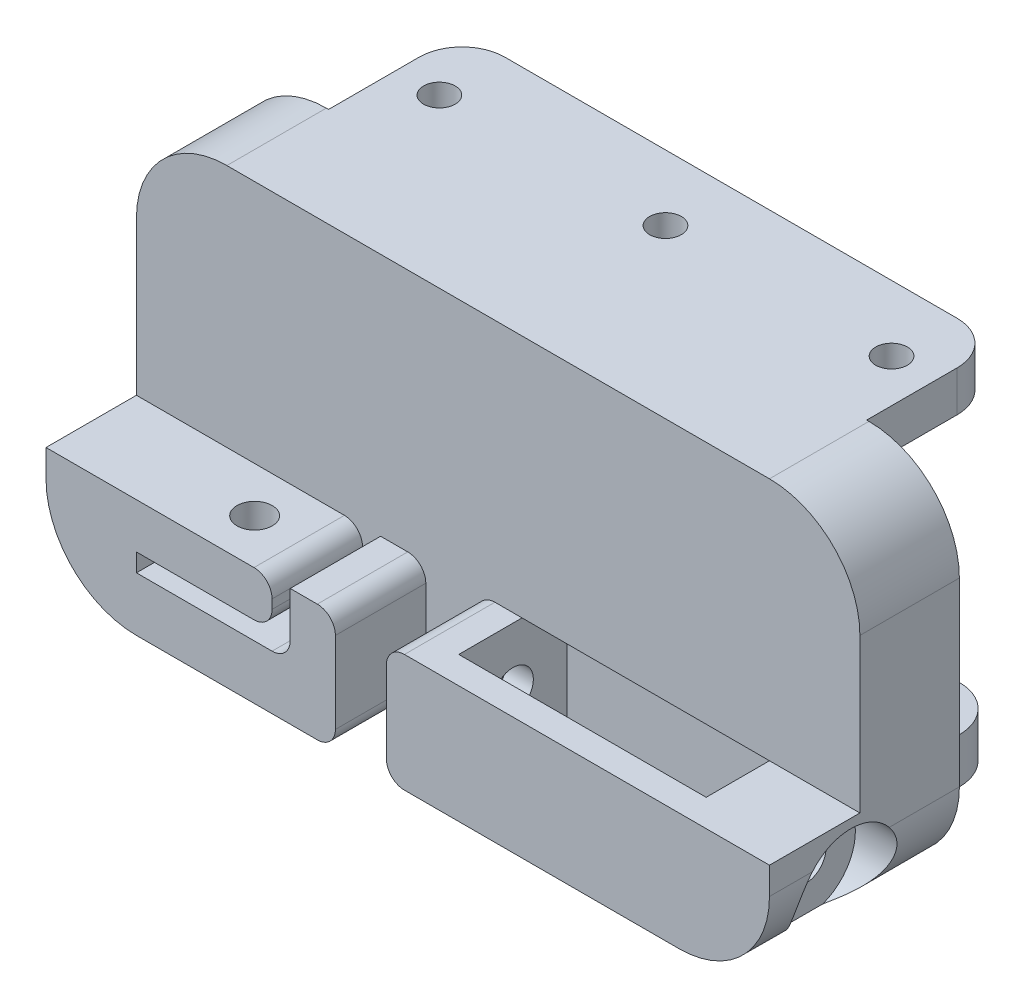
SolidWorks part; units mm, degrees
ref_plane "Front Plane" through (0, 0, 0) normal (0, 0, 1) x (1, 0, 0)
ref_plane "Top Plane" through (0, 0, 0) normal (0, 1, 0) x (1, 0, 0)
ref_plane "Right Plane" through (0, 0, 0) normal (1, 0, 0) x (0, 0, -1)
sketch "Sketch1" plane through (0, 0, 0) normal (0, 0, 1) x (1, 0, 0)
  line L0 (60, 35) -> (0, 35)
  line L1 (0, 35) -> (0, 40)
  line L2 (-10, 30) -> (-10, 10)
  line L3 (0, 0) -> (60, 0)
  line L4 (70, 10) -> (70, 30)
  line L5 (60, 40) -> (60, 35)
  arc A0 (0, 40) -> (-10, 30) centre (0, 30) ccw
  arc A1 (-10, 10) -> (0, 0) centre (0, 10) ccw
  arc A2 (60, 0) -> (70, 10) centre (60, 10) ccw
  arc A3 (70, 30) -> (60, 40) centre (60, 30) ccw
extrude "Boss-Extrude1" add sketch "Sketch1" along normal blind 11
sketch "Sketch2" plane through (0, 0, 11) normal (0, 0, 1) x (1, 0, 0)
  line L1 (0, 35) -> (60, 35)
  line L2 (0, 35) -> (0, 40)
  line L3 (0, 40) -> (60, 40)
  line L4 (60, 35) -> (60, 40)
extrude "Boss-Extrude2" add sketch "Sketch2" against normal blind 26
fillet "Fillet1" radius 5 2 edges at (60, 37.5, -15) (0, 37.5, -15)
sketch "Sketch4" plane through (0, 35, 0) normal (0, -1, 0) x (-1, 0, 0)
  line L0 (-55, 15) -> (-55, 7.5) construction
  line L1 (-30, 15) -> (-30, 7.5) construction
  line L2 (-5, 15) -> (-55, 15) construction
  line L3 (-5, 15) -> (-5, 7.5) construction
  arc A0 (0, 10) -> (-5, 15) centre (-5, 10) ccw construction
  circle A1 centre (-55, 7.5) radius 1.75
  circle A2 centre (-30, 7.5) radius 1.75
  circle A3 centre (-5, 7.5) radius 1.75
  dimension "D2" = 3.5
  dimension "D1" = 7.5
extrude "Cut-Extrude2" cut sketch "Sketch4" against normal blind 25
sketch "Sketch5" plane through (0, 35, 0) normal (0, -1, 0) x (1, 0, 0)
  line L0 (5, -14.75) -> (55, -14.75)
  line L1 (59.75, -10) -> (59.75, -0.25)
  line L3 (0.25, -0.25) -> (0.25, -10)
  line L4 (5, -15) -> (55, -15)
  line L5 (60, -10) -> (60, 0)
  line L6 (60, 0) -> (0, 0)
  line L7 (0, 0) -> (0, -10)
  line L8 (5, -15) -> (55, -15)
  line L9 (60, -10) -> (60, 0)
  line L10 (60, 0) -> (59.75, 0)
  line L11 (0, 0) -> (0, -10)
  line L12 (59.75, -0.25) -> (59.75, 0)
  line L13 (0.25, -0.25) -> (0.25, 0)
  line L14 (0.25, 0) -> (0, 0)
  line L16 (60, 0) -> (0, 0) construction
  line L17 (59.75, -0.25) -> (0.25, -0.25) construction
  arc A0 (55, -14.75) -> (59.75, -10) centre (55, -10) ccw
  arc A1 (0.25, -10) -> (5, -14.75) centre (5, -10) ccw
  arc A2 (55, -15) -> (60, -10) centre (55, -10) ccw
  arc A3 (0, -10) -> (5, -15) centre (5, -10) ccw
  arc A4 (55, -15) -> (60, -10) centre (55, -10) ccw
  arc A5 (0, -10) -> (5, -15) centre (5, -10) ccw
  dimension "D1" = 0
  dimension "D2" = 0.25
extrude "Cut-Extrude3" cut sketch "Sketch5" against normal blind 25
ref_plane "Plane1" through (0, 20, 0) normal (0, -1, 0) x (-1, 0, 0)
mirror "Mirror1" about plane through (0, 20, 0) normal (0, -1, 0) of "Cut-Extrude2", "Fillet1", "Boss-Extrude2"
sketch "Sketch16" plane through (0, 35, 0) normal (0, -1, 0) x (1, 0, 0)
  line L4 (0.25, 0) -> (0.25, -10)
  line L5 (5, -14.75) -> (55, -14.75)
  line L6 (59.75, -10) -> (59.75, 0)
  line L7 (59.75, 0) -> (0.25, 0)
  line L8 (0.25, 0) -> (0.25, -10)
  line L9 (5, -14.75) -> (55, -14.75)
  line L10 (59.75, -10) -> (59.75, 0)
  line L11 (59.75, 0) -> (0.25, 0)
  arc A2 (0.25, -10) -> (5, -14.75) centre (5, -10) ccw
  arc A3 (55, -14.75) -> (59.75, -10) centre (55, -10) ccw
  arc A4 (0.25, -10) -> (5, -14.75) centre (5, -10) ccw
  arc A5 (55, -14.75) -> (59.75, -10) centre (55, -10) ccw
  dimension "D1" = 0
extrude "Cut-Extrude7" cut sketch "Sketch16" against normal blind 0.5
sketch "Sketch19" plane through (0, 0, 11) normal (0, 0, 1) x (1, 0, 0)
  line L0 (70, 25) -> (-10, 25) construction
  line L1 (70, 10) -> (70, 30) construction
  line L2 (-10, 30) -> (-10, 10) construction
  line L3 (-10, 13) -> (15, 13)
  line L4 (15, 13) -> (15, 9.9954)
  line L5 (13, 7.9954) -> (0, 7.9954)
  line L6 (0, 7.9954) -> (0, 5.9954)
  line L7 (0, 5.9954) -> (15, 5.9954)
  line L8 (17, 7.9954) -> (17, 13)
  line L9 (17, 13) -> (22, 13)
  line L10 (22, 13) -> (22, 0)
  line L11 (0, 0) -> (60, 0) construction
  line L12 (22, 0) -> (0, 0)
  line L13 (-10, 10) -> (-10, 13)
  arc A0 (0, 0) -> (-10, 10) centre (0, 10) cw
  arc A1 (15, 5.9954) -> (17, 7.9954) centre (15, 7.9954) ccw
  arc A2 (15, 9.9954) -> (13, 7.9954) centre (13, 9.9954) cw
  point P6 (70, 20)
  point P27 (-10, 20)
  dimension "D7" = 2
  dimension "D1" = 5
  dimension "D2" = 7
  dimension "D3" = 2
  dimension "D4" = 2
  dimension "D5" = 25
  dimension "D6" = 5
extrude "Boss-Extrude3" add sketch "Sketch19" along normal blind 10
sketch "Sketch20" plane through (0, 0, 0) normal (0, -1, 0) x (-1, 0, 0)
  line L0 (-8.0687, -21) -> (-8.0687, -16) construction
  line L1 (0, -21) -> (-22, -21) construction
  circle A0 centre (-8.0687, -16) radius 1.95
  dimension "D2" = 3.9
  dimension "D1" = 5
extrude "Cut-Extrude10" cut sketch "Sketch20" against normal blind 14
fillet "Fillet2" radius 2 1 edges at (15, 13, 16)
sketch "Sketch21" plane through (0, 0, 11) normal (0, 0, 1) x (1, 0, 0)
  line L0 (70, 13) -> (60, 13)
  line L1 (70, 10) -> (70, 30) construction
  line L2 (60, 13) -> (60, 0)
  line L3 (70, 13) -> (70, 10)
  line L4 (27.6385, 0) -> (27.6385, 13)
  line L5 (22, 0) -> (60, 0) construction
  line L6 (27.6385, 13) -> (32.6385, 13)
  line L7 (32.6385, 13) -> (32.6385, 0)
  line L8 (32.6385, 0) -> (27.6385, 0)
  arc A0 (70, 10) -> (60, 0) centre (60, 10) cw
  dimension "D1" = 5
extrude "Boss-Extrude4" add sketch "Sketch21" along normal blind 10
fillet "Fillet3" radius 2 1 edges at (27.6385, 13, 16)
fillet "Fillet4" radius 2 1 edges at (27.6385, 0, 16)
sketch "Sketch24" plane through (0, 0, 11) normal (0, 0, 1) x (1, 0, 0)
  line L1 (60, 0) -> (32.6385, 0)
  line L2 (60, 0) -> (60, 13)
  line L3 (60, 13) -> (32.6385, 13)
  line L4 (32.6385, 0) -> (32.6385, 13)
extrude "Cut-Extrude12" cut sketch "Sketch24" against normal blind 5
sketch "Sketch22" plane through (32.6385, 0, 0) normal (1, 0, 0) x (0, 0, -1)
  line L1 (-6, 13) -> (-6, 0) construction
  circle A0 centre (-12, 6.5) radius 2.25
  point P8 (-6, 6.5)
  dimension "D1" = 4.5
  dimension "D3" = 6
extrude "Cut-Extrude11" cut sketch "Sketch22" against normal blind 3 and the other way through all
sketch "Sketch23" plane through (70, 0, 0) normal (1, 0, 0) x (0, 0, -1)
  circle A0 centre (-12, 6.5) radius 5.5
  dimension "D1" = 11
extrude "Cut-Extrude13" cut sketch "Sketch23" against normal blind 5
sketch "Sketch25" plane through (0, 0, 21) normal (0, 0, 1) x (1, 0, 0)
  line L0 (60, 0) -> (32.6385, 0)
  line L1 (60, 13) -> (32.6385, 13)
  line L3 (70, 10) -> (70, 13)
  line L4 (70, 13) -> (60, 13)
  line L5 (60, 13) -> (60, 0)
  line L6 (70, 10) -> (70, 13)
  line L7 (70, 13) -> (60, 13)
  line L10 (27.6385, 11) -> (27.6385, 2)
  line L11 (29.6385, 0) -> (32.6385, 0)
  line L12 (32.6385, 0) -> (32.6385, 13)
  line L13 (32.6385, 13) -> (29.6385, 13)
  line L14 (27.6385, 11) -> (27.6385, 2)
  line L15 (29.6385, 0) -> (32.6385, 0)
  line L17 (32.6385, 13) -> (29.6385, 13)
  arc A1 (60, 0) -> (70, 10) centre (60, 10) ccw
  arc A2 (60, 0) -> (70, 10) centre (60, 10) ccw
  arc A4 (27.6385, 2) -> (29.6385, 0) centre (29.6385, 2) ccw
  arc A5 (29.6385, 13) -> (27.6385, 11) centre (29.6385, 11) ccw
  arc A6 (27.6385, 2) -> (29.6385, 0) centre (29.6385, 2) ccw
  arc A7 (29.6385, 13) -> (27.6385, 11) centre (29.6385, 11) ccw
  dimension "D1" = 0
  dimension "D2" = 0
extrude "Boss-Extrude5" add sketch "Sketch25" against normal offset from surface (3 mm away) 12 up to face at (46.3192, 6.5, 6)
fillet "Fillet5" radius 2 2 edges at (22, 0, 16) (22, 13, 16)
